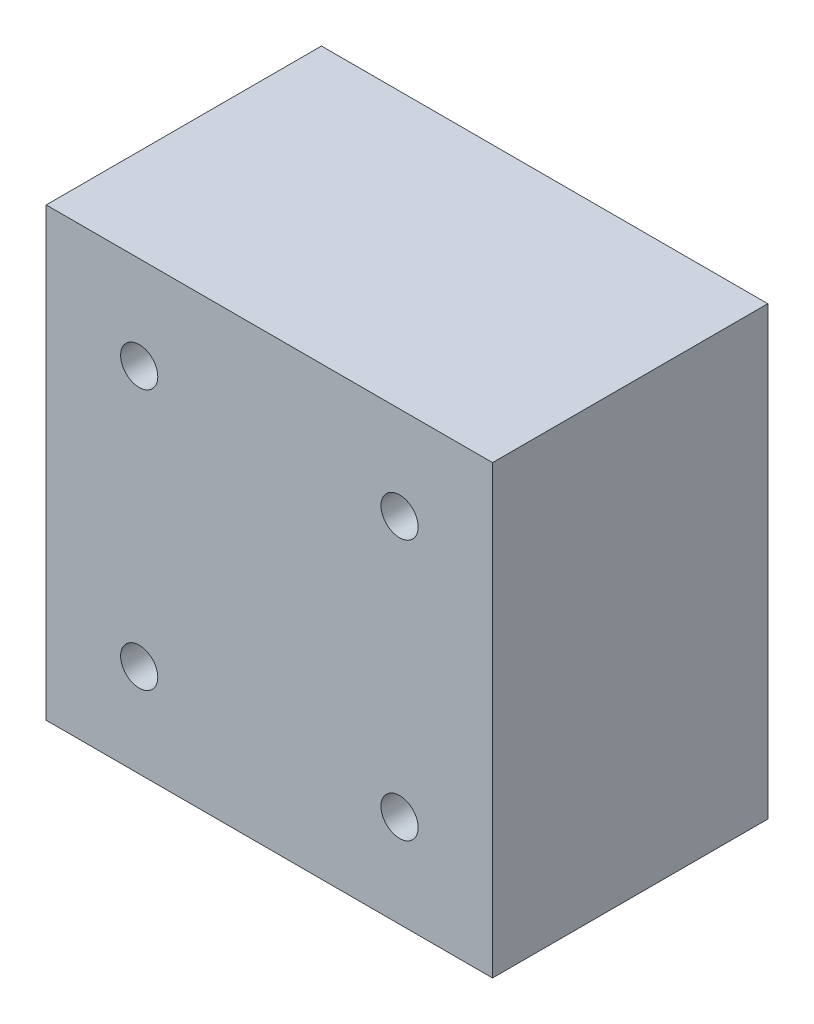
SolidWorks part; units mm, degrees
material "5052-H36"
ref_plane "Front Plane" through (0, 0, 0) normal (0, 0, 1) x (1, 0, 0)
ref_plane "Top Plane" through (0, 0, 0) normal (0, 1, 0) x (1, 0, 0)
ref_plane "Right Plane" through (0, 0, 0) normal (1, 0, 0) x (0, 0, -1)
sketch "Sketch1" plane through (0, 0, 0) normal (0, 0, 1) x (1, 0, 0)
  line L1 (-30, 30) -> (30, 30)
  line L2 (-30, 30) -> (-30, -30)
  line L3 (-30, -30) -> (30, -30)
  line L4 (30, 30) -> (30, -30)
  line L5 (-30, 30) -> (30, -30) construction
  line L6 (-30, -30) -> (30, 30) construction
  point P0 (0, 0)
  dimension "D1" = 60
  dimension "D2" = 60
extrude "Boss-Extrude1" add sketch "Sketch1" along normal blind 37
sketch "Sketch2" plane through (0, 0, 37) normal (0, 0, 1) x (1, 0, 0)
  line L0 (30, -30) -> (30, 30) construction
  line L4 (-30, -30) -> (30, -30) construction
  circle A0 centre (-17.5, 17.5) radius 2.5
  circle A1 centre (17.5, 17.5) radius 2.5
  circle A2 centre (17.5, -17.5) radius 2.5
  circle A3 centre (-17.5, -17.5) radius 2.5
  dimension "D1" = 5
  dimension "D2" = 5
  dimension "D3" = 5
  dimension "D4" = 5
  dimension "D5" = 35
  dimension "D6" = 35
  dimension "D7" = 35
  dimension "D8" = 35
  dimension "D9" = 12.5
  dimension "D10" = 12.5
  dimension "D11" = 12.5
  dimension "D12" = 12.5
extrude "Cut-Extrude1" cut sketch "Sketch2" against normal blind 60
